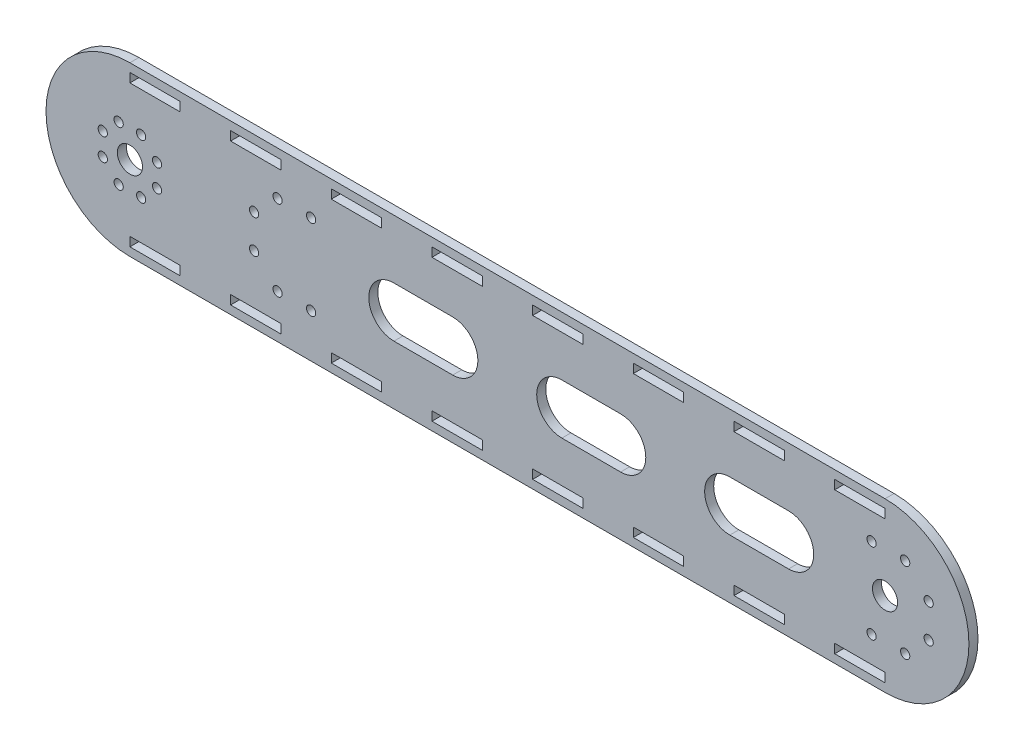
SolidWorks part; units mm, degrees
ref_plane "Front Plane" through (0, 0, 0) normal (0, 0, 1) x (1, 0, 0)
ref_plane "Top Plane" through (0, 0, 0) normal (0, 1, 0) x (1, 0, 0)
ref_plane "Right Plane" through (0, 0, 0) normal (1, 0, 0) x (0, 0, -1)
sketch "Sketch3" plane through (0, 0, 0) normal (0, 0, 1) x (1, 0, 0)
  line L0 (-242.5, 0) -> (207.5, 0) construction
  line L1 (-242.5, 50) -> (207.5, 50)
  line L2 (-242.5, -50) -> (207.5, -50)
  line L6 (115, 0) -> (150, 0) construction
  line L7 (115, 15) -> (150, 15)
  line L8 (115, -15) -> (150, -15)
  line L9 (-242.5, 0) -> (-226.3321, 6.697)
  line L10 (-242.5, 0) -> (-226.3321, 6.697) construction
  line L11 (-242.5, 0) -> (-226.3321, -6.697) construction
  line L36 (-101.4371, 0) -> (436.7316, 0) construction
  line L64 (-242.5, 45) -> (-212.5, 45)
  line L67 (-212.5, 45) -> (-212.5, 39.6)
  line L69 (32.5, 50) -> (32.5, -50) construction
  line L71 (-182.5, 45) -> (-152.5, 45)
  line L72 (-242.5, 39.6) -> (-212.5, 39.6)
  line L73 (-152.5, 45) -> (-152.5, 39.6)
  line L74 (14.924, 0) -> (49.924, 0) construction
  line L75 (14.924, 15) -> (49.924, 15)
  line L78 (14.924, -15) -> (49.924, -15)
  line L79 (-85.152, 0) -> (-50.152, 0) construction
  line L80 (-85.152, 15) -> (-50.152, 15)
  line L81 (-85.152, -15) -> (-50.152, -15)
  line L82 (-242.5, 45) -> (-242.5, 39.6)
  line L91 (-292.5, 0) -> (-17.5, 0) construction
  line L96 (-182.5, 39.6) -> (-152.5, 39.6)
  line L97 (-182.5, 45) -> (-182.5, 39.6)
  line L98 (-122.5, 45) -> (-92.5, 45)
  line L99 (-92.5, 45) -> (-92.5, 39.6)
  line L100 (-122.5, 39.6) -> (-92.5, 39.6)
  line L101 (-122.5, 45) -> (-122.5, 39.6)
  line L102 (-62.5, 45) -> (-32.5, 45)
  line L103 (-32.5, 45) -> (-32.5, 39.6)
  line L104 (-62.5, 39.6) -> (-32.5, 39.6)
  line L105 (-62.5, 45) -> (-62.5, 39.6)
  line L106 (-2.5, 45) -> (27.5, 45)
  line L107 (27.5, 45) -> (27.5, 39.6)
  line L108 (-2.5, 39.6) -> (27.5, 39.6)
  line L109 (-2.5, 45) -> (-2.5, 39.6)
  line L110 (57.5, 45) -> (87.5, 45)
  line L111 (87.5, 45) -> (87.5, 39.6)
  line L112 (57.5, 39.6) -> (87.5, 39.6)
  line L113 (57.5, 45) -> (57.5, 39.6)
  line L114 (117.5, 45) -> (147.5, 45)
  line L115 (147.5, 45) -> (147.5, 39.6)
  line L116 (117.5, 39.6) -> (147.5, 39.6)
  line L117 (117.5, 45) -> (117.5, 39.6)
  line L118 (177.5, 45) -> (207.5, 45)
  line L119 (207.5, 45) -> (207.5, 39.6)
  line L120 (177.5, 39.6) -> (207.5, 39.6)
  line L121 (177.5, 45) -> (177.5, 39.6)
  line L122 (177.5, -45) -> (177.5, -39.6)
  line L123 (177.5, -39.6) -> (207.5, -39.6)
  line L124 (207.5, -45) -> (207.5, -39.6)
  line L125 (177.5, -45) -> (207.5, -45)
  line L126 (117.5, -45) -> (117.5, -39.6)
  line L127 (117.5, -39.6) -> (147.5, -39.6)
  line L128 (147.5, -45) -> (147.5, -39.6)
  line L129 (117.5, -45) -> (147.5, -45)
  line L130 (57.5, -45) -> (57.5, -39.6)
  line L131 (57.5, -39.6) -> (87.5, -39.6)
  line L132 (87.5, -45) -> (87.5, -39.6)
  line L133 (57.5, -45) -> (87.5, -45)
  line L134 (-2.5, -45) -> (-2.5, -39.6)
  line L135 (-2.5, -39.6) -> (27.5, -39.6)
  line L136 (27.5, -45) -> (27.5, -39.6)
  line L137 (-2.5, -45) -> (27.5, -45)
  line L138 (-62.5, -45) -> (-62.5, -39.6)
  line L139 (-62.5, -39.6) -> (-32.5, -39.6)
  line L140 (-32.5, -45) -> (-32.5, -39.6)
  line L141 (-62.5, -45) -> (-32.5, -45)
  line L142 (-122.5, -45) -> (-122.5, -39.6)
  line L143 (-122.5, -39.6) -> (-92.5, -39.6)
  line L144 (-92.5, -45) -> (-92.5, -39.6)
  line L145 (-122.5, -45) -> (-92.5, -45)
  line L146 (-182.5, -45) -> (-182.5, -39.6)
  line L147 (-182.5, -39.6) -> (-152.5, -39.6)
  line L148 (-152.5, -45) -> (-152.5, -39.6)
  line L149 (-182.5, -45) -> (-152.5, -45)
  line L150 (-242.5, -45) -> (-242.5, -39.6)
  line L151 (-242.5, -39.6) -> (-212.5, -39.6)
  line L152 (-212.5, -45) -> (-212.5, -39.6)
  line L153 (-242.5, -45) -> (-212.5, -45)
  arc A0 (-242.5, 50) -> (-242.5, -50) centre (-242.5, 0) ccw
  arc A1 (207.5, -50) -> (207.5, 50) centre (207.5, 0) ccw
  circle A2 centre (-242.5, 0) radius 7.5
  circle A3 centre (207.5, 0) radius 7.5
  arc A6 (115, 15) -> (115, -15) centre (115, 0) ccw
  arc A7 (150, -15) -> (150, 15) centre (150, 0) ccw
  circle A8 centre (-226.3321, 6.697) radius 2.75
  circle A9 centre (-226.3321, -6.697) radius 2.75
  circle A10 centre (-235.803, -16.1679) radius 2.75
  circle A11 centre (-249.197, -16.1679) radius 2.75
  circle A12 centre (-258.6679, -6.697) radius 2.75
  circle A13 centre (-258.6679, 6.697) radius 2.75
  circle A14 centre (-249.197, 16.1679) radius 2.75
  circle A15 centre (-235.803, 16.1679) radius 2.75
  circle A41 centre (-134.5, -24) radius 2.75
  circle A42 centre (-154.5, -24) radius 2.75
  circle A43 centre (-168.5, -10) radius 2.75
  circle A44 centre (-168.5, 10) radius 2.75
  circle A45 centre (-154.5, 24) radius 2.75
  circle A46 centre (-134.5, 24) radius 2.75
  arc A49 (14.924, 15) -> (14.924, -15) centre (14.924, 0) ccw
  arc A50 (49.924, -15) -> (49.924, 15) centre (49.924, 0) ccw
  arc A51 (-85.152, 15) -> (-85.152, -15) centre (-85.152, 0) ccw
  arc A52 (-50.152, -15) -> (-50.152, 15) centre (-50.152, 0) ccw
  circle A53 centre (199.5, -24) radius 2.75
  circle A54 centre (219.5, -24) radius 2.75
  circle A55 centre (233.5, -10) radius 2.75
  circle A56 centre (233.5, 10) radius 2.75
  circle A57 centre (219.5, 24) radius 2.75
  circle A58 centre (199.5, 24) radius 2.75
  point P3 (-17.5, 0)
  point P19 (132.5, 0)
  point P68 (32.424, 0)
  point P75 (-67.652, 0)
  dimension "D2" = 50
  dimension "D3" = 15
  dimension "D4" = 15
  dimension "D7" = 5.5
  dimension "D27" = 15
  dimension "D1" = 450
  dimension "D5" = 17.5
  dimension "D6" = 22.5
  dimension "D9" = 45
  dimension "D10" = 0
  dimension "D11" = 5
  dimension "D12" = 8
  dimension "D15" = 3
  dimension "D26" = 35
  dimension "D29" = 150
  dimension "D30" = 175
  dimension "D13" = 5.4
  dimension "D8" = 8
extrude "Boss-Extrude1" add sketch "Sketch3" along normal blind 5.4
